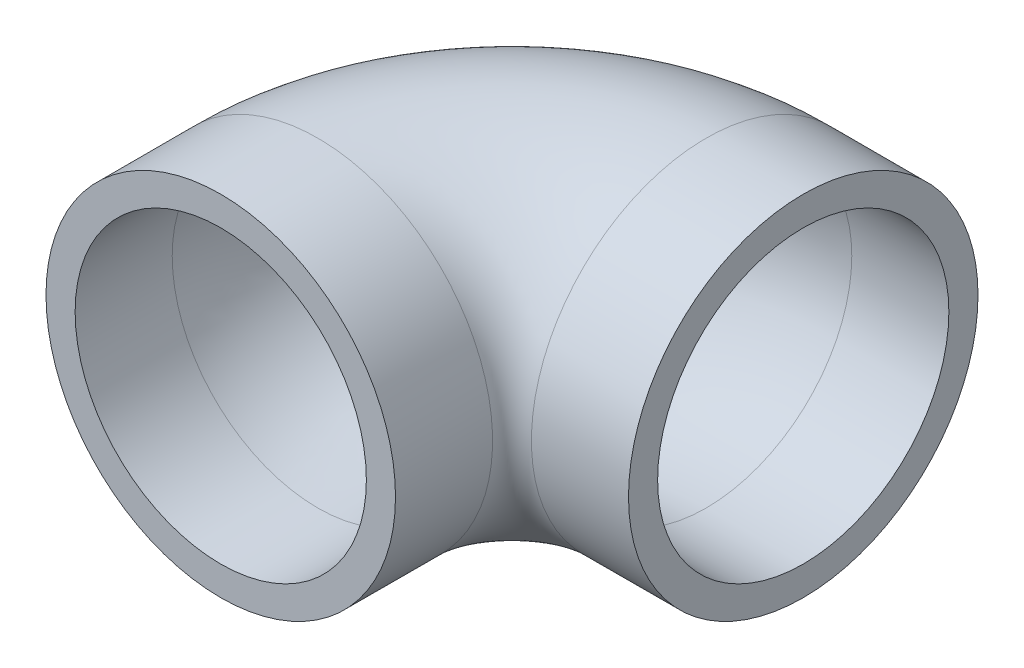
SolidWorks part; units mm, degrees
material "PVC Rigid"
ref_plane "Front Plane" through (0, 0, 0) normal (0, 0, 1) x (1, 0, 0)
ref_plane "Top Plane" through (0, 0, 0) normal (0, 1, 0) x (1, 0, 0)
ref_plane "Right Plane" through (0, 0, 0) normal (1, 0, 0) x (0, 0, -1)
sketch "Sketch1" plane through (0, 0, 0) normal (0, 0, 1) x (1, 0, 0)
  circle A0 centre (0, 0) radius 22.86
  circle A1 centre (0, 0) radius 19.05
  dimension "D1" = 38.1
  dimension "D2" = 45.72
sketch "Sketch3" plane through (0, 0, 0) normal (0, 1, 0) x (1, 0, 0)
  line L0 (0, 0) -> (0, 12.7)
  line L1 (25.4, 38.1) -> (38.1, 38.1)
  arc A0 (0, 12.7) -> (25.4, 38.1) centre (25.4, 12.7) cw
  dimension "D2" = 25.4
  dimension "D1" = 12.7
sweep "Sweep1" add profiles "Sketch1" path "Sketch3"
